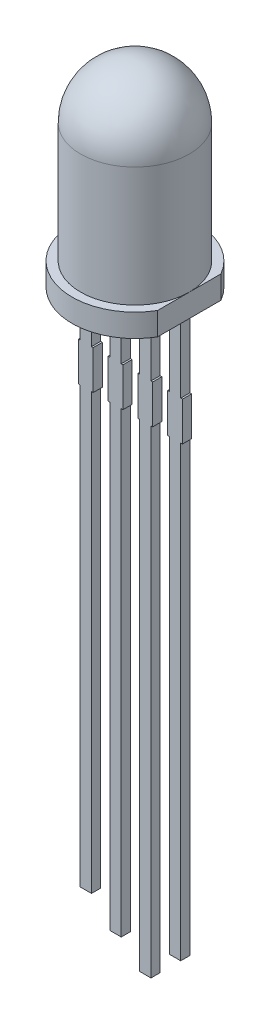
SolidWorks part; units mm, degrees
ref_plane "Front" through (0, 0, 0) normal (0, 0, 1) x (1, 0, 0)
ref_plane "Top" through (0, 0, 0) normal (0, 1, 0) x (1, 0, 0)
ref_plane "Right" through (0, 0, 0) normal (1, 0, 0) x (0, 0, -1)
sketch "Sketch1" plane through (0, 0, 0) normal (0, 0, 1) x (1, 0, 0)
  line L0 (0, 0) -> (0, -2989.7799) construction
  line L1 (0, 0) -> (2.75, 0)
  line L2 (2.75, 0) -> (2.75, 1)
  line L3 (2.75, 1) -> (2.375, 1)
  line L4 (2.375, 1) -> (2.375, 6.225)
  line L5 (0, 8.6) -> (0, 0)
  arc A0 (2.375, 6.225) -> (0, 8.6) centre (0, 6.225) ccw
  point P10 (0, 0)
  dimension "D1" = 4.75
  dimension "D2" = 1
  dimension "D3" = 5.5
  dimension "D4" = 8.6
revolve "Revolve1" add sketch "Sketch1" angle 360 about L0
sketch "Sketch2" plane through (0, 0, 0) normal (0, 0, 1) x (1, 0, 0)
  line L0 (-2.75, 0) -> (2.75, 0) construction
  line L1 (2.2, -24.3) -> (1.7, -24.3)
  line L2 (2.2, -24.3) -> (2.2, 0)
  line L3 (2.2, 0) -> (1.7, 0)
  line L4 (1.7, -24.3) -> (1.7, 0)
  line L5 (2.2, -24.3) -> (1.7, 0) construction
  line L6 (2.2, 0) -> (1.7, -24.3) construction
  line L7 (0, 0) -> (0, -50000) construction
  line L8 (0.9, -25.6) -> (0.4, -25.6)
  line L9 (0.9, -25.6) -> (0.9, 0)
  line L10 (0.9, 0) -> (0.4, 0)
  line L11 (0.4, -25.6) -> (0.4, 0)
  line L12 (0.9, -25.6) -> (0.4, 0) construction
  line L13 (0.9, 0) -> (0.4, -25.6) construction
  line L14 (-0.4, -24.7) -> (-0.9, -24.7)
  line L15 (-0.4, -24.7) -> (-0.4, 0)
  line L16 (-0.4, 0) -> (-0.9, 0)
  line L17 (-0.9, -24.7) -> (-0.9, 0)
  line L18 (-0.4, -24.7) -> (-0.9, 0) construction
  line L19 (-0.4, 0) -> (-0.9, -24.7) construction
  line L20 (-1.7, -23.7) -> (-2.2, -23.7)
  line L21 (-1.7, -23.7) -> (-1.7, 0)
  line L22 (-1.7, 0) -> (-2.2, 0)
  line L23 (-2.2, -23.7) -> (-2.2, 0)
  line L24 (-1.7, -23.7) -> (-2.2, 0) construction
  line L25 (-1.7, 0) -> (-2.2, -23.7) construction
  line L26 (1.95, 0) -> (0.65, 0) construction
  line L27 (0.65, 0) -> (-0.65, 0) construction
  line L29 (-1.625, -3) -> (-2.275, -3)
  line L30 (-1.625, -3) -> (-1.625, -4.7)
  line L31 (-1.625, -4.7) -> (-2.275, -4.7)
  line L32 (-2.275, -3) -> (-2.275, -4.7)
  line L33 (-1.625, -3) -> (-2.275, -4.7) construction
  line L34 (-1.625, -4.7) -> (-2.275, -3) construction
  line L35 (-0.325, -3) -> (-0.975, -3)
  line L36 (-0.325, -3) -> (-0.325, -4.7)
  line L37 (-0.325, -4.7) -> (-0.975, -4.7)
  line L38 (-0.975, -3) -> (-0.975, -4.7)
  line L39 (-0.325, -3) -> (-0.975, -4.7) construction
  line L40 (-0.325, -4.7) -> (-0.975, -3) construction
  line L41 (0.975, -3) -> (0.325, -3)
  line L42 (0.975, -3) -> (0.975, -4.7)
  line L43 (0.975, -4.7) -> (0.325, -4.7)
  line L44 (0.325, -3) -> (0.325, -4.7)
  line L45 (0.975, -3) -> (0.325, -4.7) construction
  line L46 (0.975, -4.7) -> (0.325, -3) construction
  line L47 (2.275, -3) -> (1.625, -3)
  line L48 (2.275, -3) -> (2.275, -4.7)
  line L49 (2.275, -4.7) -> (1.625, -4.7)
  line L50 (1.625, -3) -> (1.625, -4.7)
  line L51 (2.275, -3) -> (1.625, -4.7) construction
  line L52 (2.275, -4.7) -> (1.625, -3) construction
  point P0 (1.95, -12.15)
  point P7 (0.65, -12.8)
  point P12 (-0.65, -12.35)
  point P17 (-1.95, -11.85)
  point P27 (-1.95, -3.85)
  point P28 (0.65, 0)
  point P29 (1.95, 0)
  point P35 (-0.65, -3.85)
  point P40 (0.65, -3.85)
  point P45 (1.95, -3.85)
  point P50 (0, 0)
  point P51 (-1.95, 0)
  point P52 (0, 0)
  point P53 (0, 0)
  point P54 (0, 0)
  point P55 (0, 0)
  dimension "D1" = 0.5
  dimension "D2" = 1.3
  dimension "D3" = 24.3
  dimension "D4" = 25.6
  dimension "D5" = 24.7
  dimension "D6" = 23.7
  dimension "D7" = 0.65
  dimension "D8" = 1.7
  dimension "D9" = 3
extrude "Boss-Extrude1" add sketch "Sketch2" along normal mid plane 0.4 contours L32 L31 L30 L29 | L23 L22 L21 L20 | L37 L38 L35 L36 | L17 L16 L15 L14 | L43 L44 L41 L42 | L11 L10 L9 L8 | L49 L50 L47 L48 | L4 L3 L2 L1
sketch "Sketch3" plane through (0, 1, 0) normal (0, 1, 0) x (1, 0, 0)
  line L0 (2.375, 1.3863) -> (2.375, -1.3863)
  circle A0 centre (0, 0) radius 2.75 construction
  circle A1 centre (0, 0) radius 2.375 construction
  point P4 (2.3875, -1.3647)
extrude "Cut-Extrude1" cut sketch "Sketch3" against normal through all
